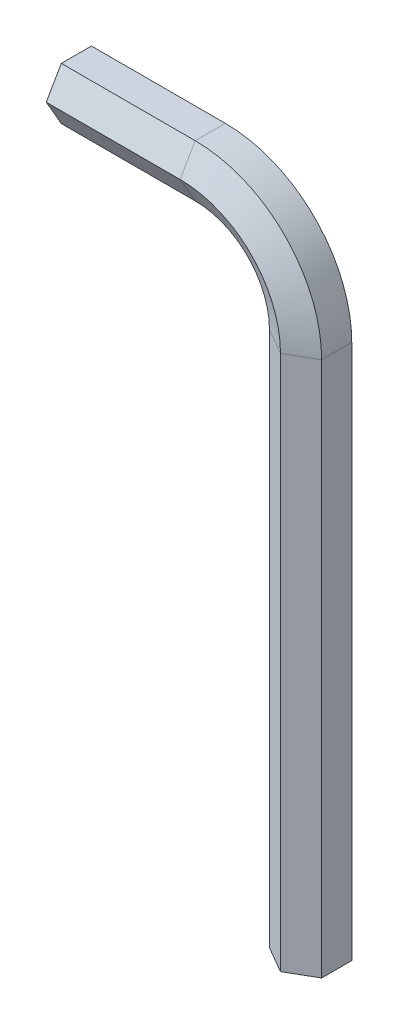
SolidWorks part; units mm, degrees
ref_plane "Front Plane" through (0, 0, 0) normal (0, 0, 1) x (1, 0, 0)
ref_plane "Top Plane" through (0, 0, 0) normal (0, 1, 0) x (1, 0, 0)
ref_plane "Right Plane" through (0, 0, 0) normal (1, 0, 0) x (0, 0, -1)
sketch "Sketch1" plane through (0, 0, 0) normal (0, 0, 1) x (1, 0, 0)
  line L0 (0, 0) -> (0, 80)
  line L1 (-15, 95) -> (-35, 95)
  arc A0 (0, 80) -> (-15, 95) centre (-15, 80) ccw
  dimension "D3" = 15
  dimension "D1" = 80
  dimension "D2" = 20
  dimension "D4" = 15
  dimension "D5" = 15
ref_plane "Plane1" through (-35, 95, 0) normal (-1, 0, 0) x (0, 0, 1)
sketch "Sketch2" plane through (-35, 95, 0) normal (-1, 0, 0) x (0, 0, 1)
  line L0 (0, -15) -> (0, 0) construction
  line L1 (4.5, 0) -> (2.25, 3.8971)
  line L2 (2.25, 3.8971) -> (-2.25, 3.8971)
  line L3 (-2.25, 3.8971) -> (-4.5, 0)
  line L4 (-4.5, 0) -> (-2.25, -3.8971)
  line L5 (-2.25, -3.8971) -> (2.25, -3.8971)
  line L6 (2.25, -3.8971) -> (4.5, 0)
  circle A0 centre (0, 0) radius 3.8971 construction
  dimension "D1" = 4.5
sweep "Sweep1" add profiles "Sketch2" path "Sketch1"
